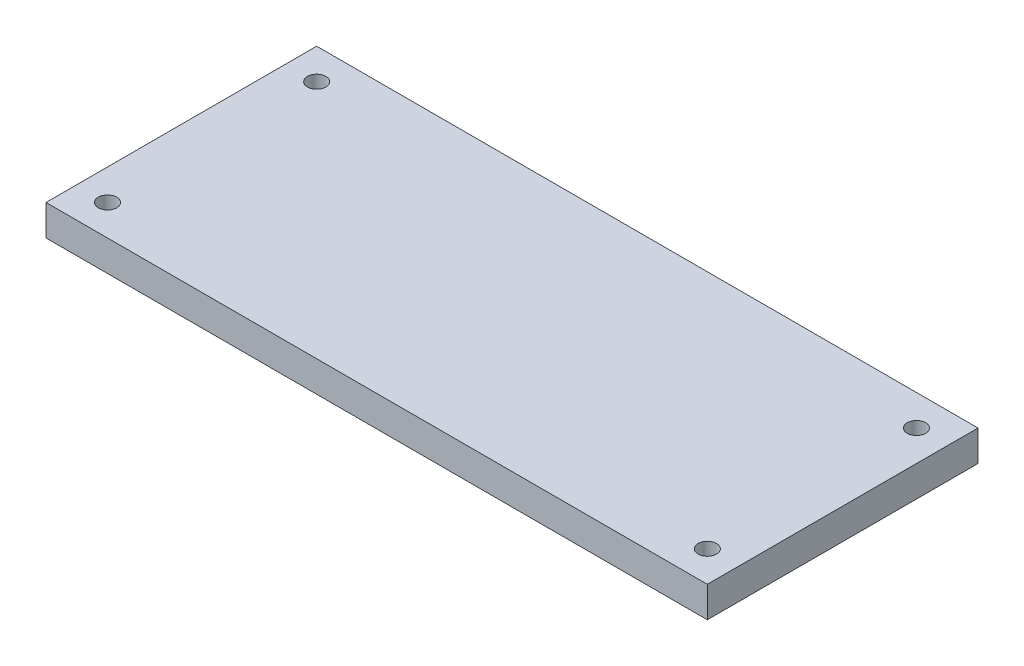
SolidWorks part; units mm, degrees
ref_plane "Front Plane" through (0, 0, 0) normal (0, 0, 1) x (1, 0, 0)
ref_plane "Top Plane" through (0, 0, 0) normal (0, 1, 0) x (1, 0, 0)
ref_plane "Right Plane" through (0, 0, 0) normal (1, 0, 0) x (0, 0, -1)
sketch "Sketch1" plane through (0, 0, 0) normal (0, 1, 0) x (1, 0, 0)
  line L1 (0, 88) -> (215, 88)
  line L2 (0, 88) -> (0, 0)
  line L3 (0, 0) -> (215, 0)
  line L4 (215, 88) -> (215, 0)
  circle A0 centre (10, 78) radius 3
  circle A1 centre (10, 10) radius 3
  circle A2 centre (205, 78) radius 3
  circle A3 centre (205, 10) radius 3
  point P12 (0, 0)
  point P13 (0, 0)
  point P14 (0, 0)
  point P15 (0, 0)
  point P16 (0, 0)
  point P17 (0, 0)
extrude "Boss-Extrude1" add sketch "Sketch1" along normal blind 10
